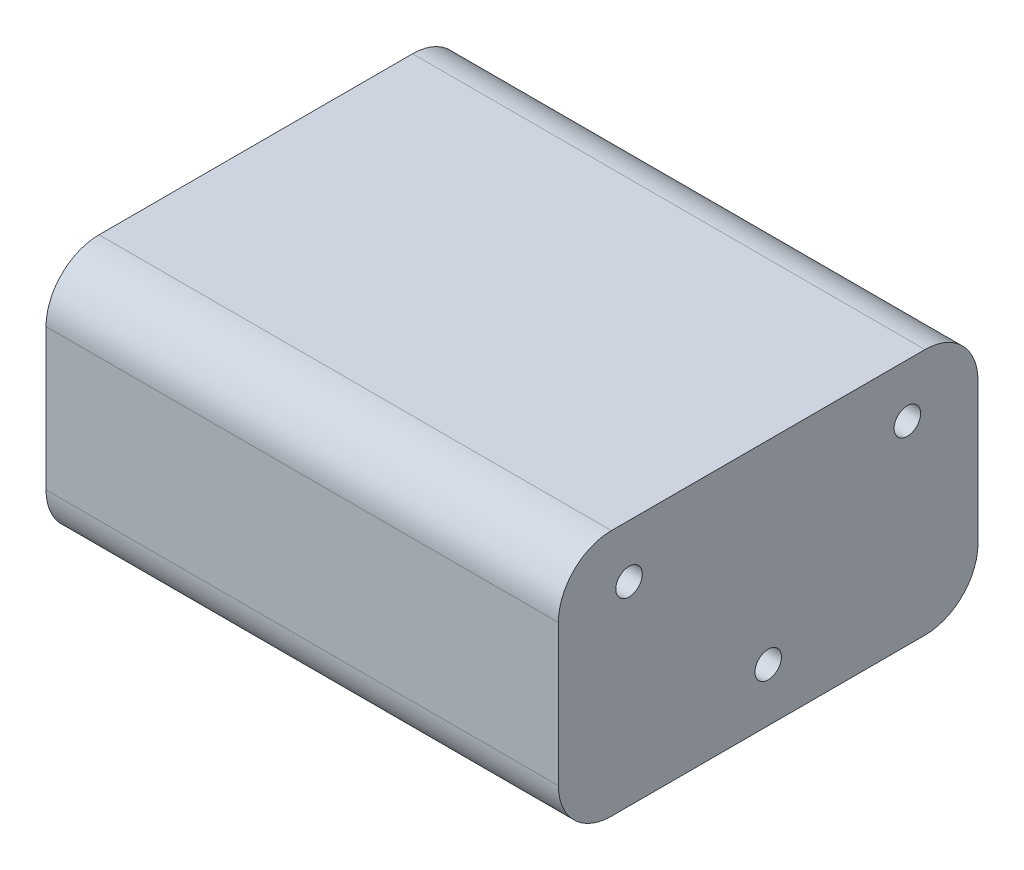
SolidWorks part; units mm, degrees
ref_plane "Front Plane" through (0, 0, 0) normal (0, 0, 1) x (1, 0, 0)
ref_plane "Top Plane" through (0, 0, 0) normal (0, 1, 0) x (1, 0, 0)
ref_plane "Right Plane" through (0, 0, 0) normal (1, 0, 0) x (0, 0, -1)
sketch "Sketch1" plane through (0, 0, 0) normal (0, 1, 0) x (1, 0, 0)
  line L1 (-29, -23.75) -> (29, -23.75)
  line L2 (-29, -23.75) -> (-29, 23.75)
  line L3 (-29, 23.75) -> (29, 23.75)
  line L4 (29, -23.75) -> (29, 23.75)
  line L5 (-29, -23.75) -> (29, 23.75) construction
  line L6 (-29, 23.75) -> (29, -23.75) construction
  point P0 (0, 0)
  dimension "D1" = 58
  dimension "D2" = 47.5
extrude "Boss-Extrude1" add sketch "Sketch1" along normal blind 28
fillet "Fillet3" radius 6 4 edges at (0, 0, -23.75) (0, 0, 23.75) (0, 28, -23.75) (0, 28, 23.75)
sketch "Sketch2" plane through (29, 0, 0) normal (1, 0, 0) x (0, 0, -1)
  line L0 (0, 15.4) -> (0, -15.4) construction
  line L1 (26.125, 0) -> (-26.125, 0) construction
  line L2 (-17.75, 28) -> (17.75, 28) construction
  line L3 (-23.75, 22) -> (-23.75, 6) construction
  line L4 (23.75, 22) -> (23.75, 6) construction
  circle A0 centre (0, 6) radius 1.5
  circle A3 centre (-15.75, 22) radius 1.5
  circle A4 centre (15.75, 22) radius 1.5
  dimension "D1" = 3
  dimension "D7" = 3
  dimension "D8" = 3
  dimension "D2" = 6
  dimension "D3" = 6
  dimension "D4" = 8
  dimension "D5" = 6
  dimension "D6" = 8
extrude "Cut-Extrude1" cut sketch "Sketch2" against normal blind 3 from surface at 0 starting at face at (29, 14, 0)
sketch "Sketch3" plane through (0, 0, 0) normal (1, 0, 0) x (0, 0, -1)
  line L0 (17.75, 28) -> (-17.75, 28) construction
  line L1 (26.125, 0) -> (-26.125, 0) construction
  line L2 (23.75, 22) -> (23.75, 6) construction
  line L3 (-23.75, 22) -> (-23.75, 6) construction
  circle A0 centre (0.1076, 22) radius 1.5
  circle A1 centre (-15.75, 6) radius 1.5
  circle A2 centre (15.75, 6) radius 1.5
  dimension "D1" = 3
  dimension "D2" = 3
  dimension "D3" = 3
  dimension "D4" = 6
  dimension "D5" = 6
  dimension "D6" = 6
  dimension "D7" = 8
  dimension "D8" = 8
extrude "Cut-Extrude2" cut sketch "Sketch3" along normal blind 3 from surface at -29 starting at face at (-29, 14, 0)
